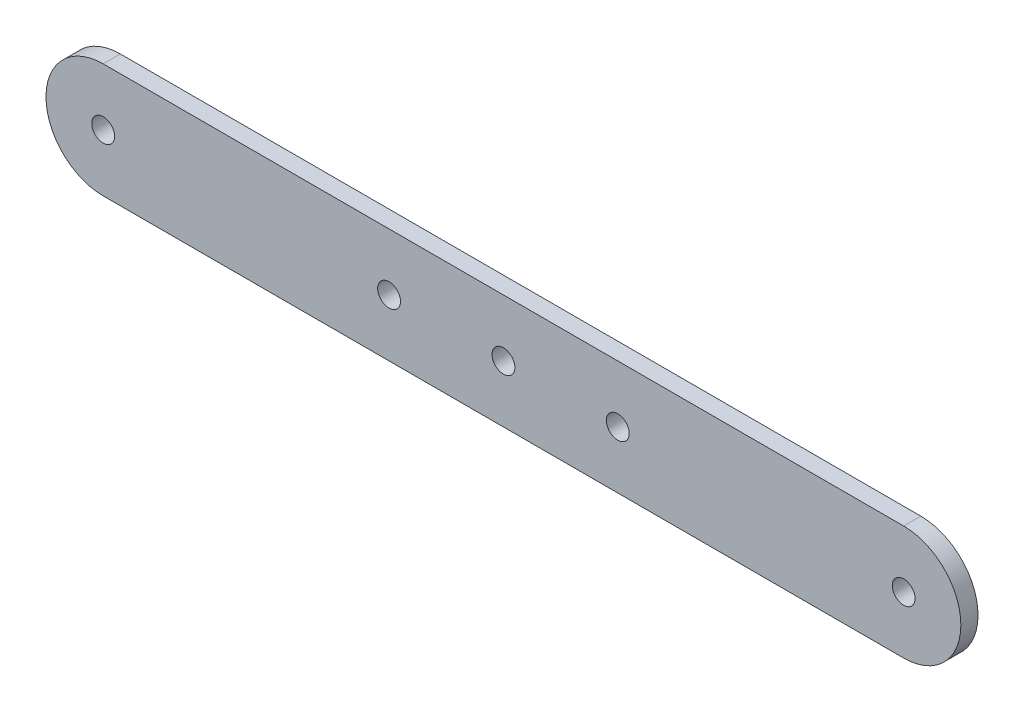
SolidWorks part; units mm, degrees
ref_plane "Plan de face" through (0, 0, 0) normal (0, 0, 1) x (1, 0, 0)
ref_plane "Plan de dessus" through (0, 0, 0) normal (0, 1, 0) x (1, 0, 0)
ref_plane "Plan de droite" through (0, 0, 0) normal (1, 0, 0) x (0, 0, -1)
sketch "Esquisse1" plane through (0, 0, 0) normal (0, 0, 1) x (1, 0, 0)
  line L0 (-35, 5) -> (35, 5)
  line L1 (0, 0) -> (0, 14.0741) construction
  line L2 (0, 0) -> (31.4758, 0) construction
  line L3 (-35, -5) -> (35, -5)
  arc A0 (-35, -5) -> (-35, 5) centre (-35, 0) cw
  arc A1 (35, -5) -> (35, 5) centre (35, 0) ccw
  circle A2 centre (-35, 0) radius 1
  circle A3 centre (0, 0) radius 1
  circle A4 centre (35, 0) radius 1
  circle A5 centre (-10, 0) radius 1
  circle A6 centre (10, 0) radius 1
  dimension "D3" = 2
  dimension "D1" = 10
  dimension "D2" = 70
  dimension "D4" = 20
extrude "Boss.-Extru.2" add sketch "Esquisse1" along normal blind 1.5 contours L0 A1 L3 A0 | A2 | A5 | A3 | A6 | A4
